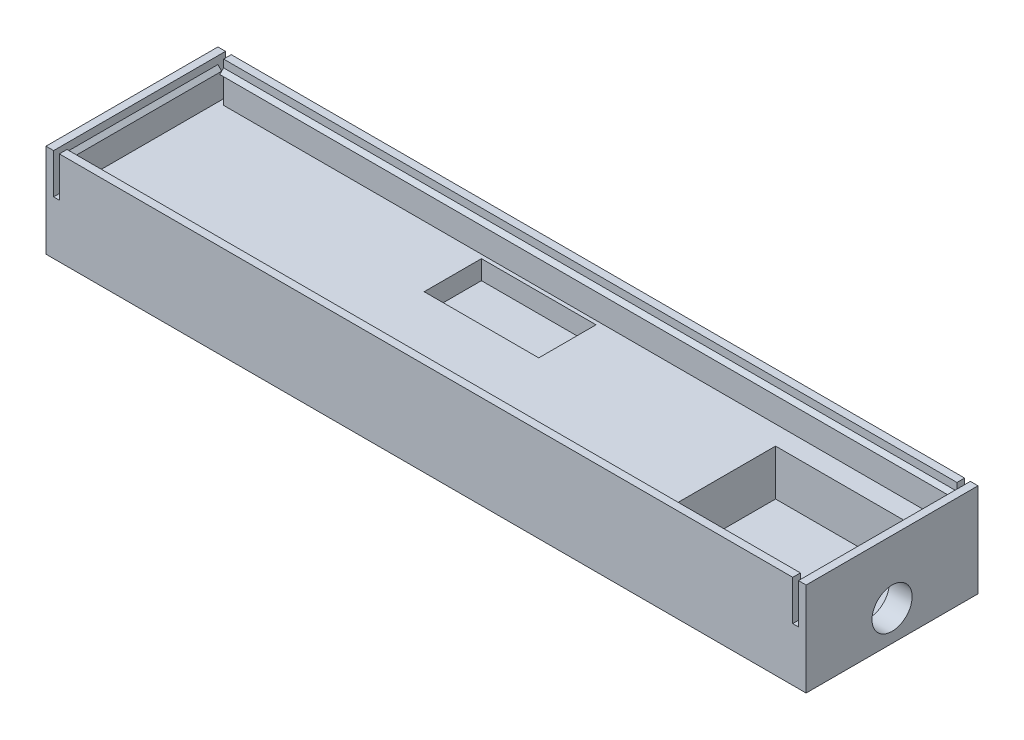
SolidWorks part; units mm, degrees
ref_plane "Front" through (0, 0, 0) normal (0, 0, 1) x (1, 0, 0)
ref_plane "Top" through (0, 0, 0) normal (0, 1, 0) x (1, 0, 0)
ref_plane "Right" through (0, 0, 0) normal (1, 0, 0) x (0, 0, -1)
sketch "Sketch1" plane through (0, 0, 0) normal (0, 1, 0) x (1, 0, 0)
  line L1 (-99.5, 22.5) -> (99.5, 22.5)
  line L2 (-99.5, 22.5) -> (-99.5, -22.5)
  line L3 (-99.5, -22.5) -> (99.5, -22.5)
  line L4 (99.5, 22.5) -> (99.5, -22.5)
  line L5 (-99.5, 22.5) -> (99.5, -22.5) construction
  line L6 (-99.5, -22.5) -> (99.5, 22.5) construction
  point P0 (0, 0)
  dimension "D1" = 45
  dimension "D2" = 199
extrude "Boss-Extrude1" add sketch "Sketch1" along normal blind 14
sketch "Sketch2" plane through (0, 14, 0) normal (0, 1, 0) x (1, 0, 0)
  line L0 (99.5, 22.5) -> (-99.5, 22.5) construction
  line L1 (93.5, 15.5) -> (53.5, 15.5)
  line L2 (93.5, 15.5) -> (93.5, -15.5)
  line L3 (93.5, -15.5) -> (53.5, -15.5)
  line L4 (53.5, 15.5) -> (53.5, -15.5)
  line L5 (99.5, -22.5) -> (99.5, 22.5) construction
  line L6 (-99.5, -22.5) -> (99.5, -22.5) construction
  line L8 (93.5, 15.5) -> (88.5, 15.5)
  line L9 (93.5, 15.5) -> (93.5, 10.5)
  line L10 (93.5, 10.5) -> (88.5, 10.5)
  line L11 (88.5, 15.5) -> (88.5, 10.5)
  line L12 (93.5, -15.5) -> (88.5, -15.5)
  line L13 (93.5, -15.5) -> (93.5, -10.5)
  line L14 (93.5, -10.5) -> (88.5, -10.5)
  line L15 (88.5, -15.5) -> (88.5, -10.5)
  dimension "D1" = 7
  dimension "D2" = 6
  dimension "D3" = 7
  dimension "D4" = 40
  dimension "D5" = 5
  dimension "D6" = 5
  dimension "D7" = 5
  dimension "D8" = 5
extrude "Cut-Extrude1" cut sketch "Sketch2" against normal blind 12 contours L3 L15 L14 L2 L10 L11 L1 L4
sketch "Sketch3" plane through (99.5, 0, 0) normal (1, 0, 0) x (0, 0, -1)
  line L0 (0, 0) -> (0, 50000) construction
  line L1 (-22.5, 14) -> (22.5, 14) construction
  circle A0 centre (0, 8) radius 5.25
  dimension "D1" = 10.5
  dimension "D2" = 6
extrude "Cut-Extrude2" cut sketch "Sketch3" against normal up to next
sketch "Sketch4" plane through (0, 14, 0) normal (0, 1, 0) x (1, 0, 0)
  line L0 (99.5, 22.5) -> (-99.5, 22.5) construction
  line L1 (-27.5, 19.5) -> (2.5, 19.5)
  line L2 (-27.5, 19.5) -> (-27.5, 4.5)
  line L3 (-27.5, 4.5) -> (2.5, 4.5)
  line L4 (2.5, 19.5) -> (2.5, 4.5)
  line L5 (-99.5, 22.5) -> (-99.5, -22.5) construction
  dimension "D1" = 30
  dimension "D2" = 15
  dimension "D3" = 3
  dimension "D4" = 72
extrude "Cut-Extrude3" cut sketch "Sketch4" against normal blind 5
sketch "Sketch5" plane through (0, 14, 0) normal (0, 1, 0) x (1, 0, 0)
  line L1 (-99.5, 22.5) -> (99.5, 22.5)
  line L2 (-99.5, 22.5) -> (-99.5, -22.5)
  line L3 (-99.5, -22.5) -> (99.5, -22.5)
  line L4 (99.5, 22.5) -> (99.5, -22.5)
  line L5 (-99.5, 22.5) -> (99.5, -22.5) construction
  line L6 (-99.5, -22.5) -> (99.5, 22.5) construction
  line L7 (-97.5, 20.5) -> (97.5, 20.5)
  line L8 (-97.5, 20.5) -> (-97.5, -20.5)
  line L9 (-97.5, -20.5) -> (97.5, -20.5)
  line L10 (97.5, 20.5) -> (97.5, -20.5)
  line L11 (-97.5, 20.5) -> (97.5, -20.5) construction
  line L12 (-97.5, -20.5) -> (97.5, 20.5) construction
  point P0 (0, 0)
  point P5 (0, 0)
  dimension "D1" = 2
  dimension "D2" = 2
extrude "Boss-Extrude2" add sketch "Sketch5" along normal blind 10.5
sketch "Sketch6" plane through (0, 24.5, 0) normal (0, 1, 0) x (1, 0, 0)
  line L0 (99.5, 22.5) -> (-99.5, 22.5) construction
  line L5 (-97.5, 20.5) -> (-96, 20.5)
  line L6 (-97.5, 20.5) -> (-97.5, 22.5)
  line L7 (-97.5, 22.5) -> (-96, 22.5)
  line L8 (-96, 20.5) -> (-96, 22.5)
  line L9 (0, 0) -> (0, 50000) construction
  line L10 (0, 0) -> (50000, 0) construction
  line L11 (97.5, 22.5) -> (96, 22.5)
  line L12 (96, 20.5) -> (96, 22.5)
  line L13 (97.5, 20.5) -> (96, 20.5)
  line L14 (97.5, 20.5) -> (97.5, 22.5)
  line L15 (97.5, -20.5) -> (97.5, -22.5)
  line L16 (97.5, -20.5) -> (96, -20.5)
  line L17 (96, -20.5) -> (96, -22.5)
  line L18 (97.5, -22.5) -> (96, -22.5)
  line L19 (-97.5, -22.5) -> (-96, -22.5)
  line L20 (-96, -20.5) -> (-96, -22.5)
  line L21 (-97.5, -20.5) -> (-96, -20.5)
  line L22 (-97.5, -20.5) -> (-97.5, -22.5)
  dimension "D1" = 1.5
extrude "Cut-Extrude4" cut sketch "Sketch6" against normal up to surface (10.5 mm away) up to face at (0, 14, 0)
sketch "Sketch7" plane through (0, 0, -20.5) normal (0, 0, 1) x (1, 0, 0)
  line L0 (-97.5, 22.5001) -> (-96.5, 21.5001)
  line L1 (-97.5, 14) -> (-97.5, 24.5) construction
  line L2 (-96.5, 21.5001) -> (-97.5, 20.5001)
  line L3 (-97.5, 20.5001) -> (-97.5, 22.5001)
  line L4 (-99.5, 24.5) -> (-97.5, 24.5) construction
  line L5 (0, 0) -> (0, 50000) construction
  line L6 (97.5, 20.5001) -> (97.5, 22.5001)
  line L7 (96.5, 21.5001) -> (97.5, 20.5001)
  line L8 (97.5, 22.5001) -> (96.5, 21.5001)
  dimension "D1" = 45
  dimension "D2" = 2
  dimension "D3" = 1.9999
extrude "Boss-Extrude5" add sketch "Sketch7" along normal up to surface (41 mm away) up to face at (0, 19.25, 20.5)
sketch "Sketch8" plane through (96, 0, 0) normal (1, 0, 0) x (0, 0, -1)
  line L0 (-20.5, 22.5) -> (-19.5, 21.5)
  line L1 (-20.5, 14) -> (-20.5, 24.5) construction
  line L2 (-19.5, 21.5) -> (-20.5, 20.5)
  line L3 (-20.5, 20.5) -> (-20.5, 22.5)
  line L4 (-22.5, 24.5) -> (22.5, 24.5) construction
  line L5 (0, 0) -> (0, 50000) construction
  line L6 (20.5, 20.5) -> (20.5, 22.5)
  line L7 (19.5, 21.5) -> (20.5, 20.5)
  line L8 (20.5, 22.5) -> (19.5, 21.5)
  dimension "D1" = 45
  dimension "D2" = 45
  dimension "D3" = 2
  dimension "D4" = 2
extrude "Boss-Extrude6" add sketch "Sketch8" against normal up to surface (192 mm away) up to face at (-96, 19.25, 21.5)
sketch "Sketch9" plane through (0, 0, 0) normal (0, -1, 0) x (1, 0, 0)
  line L0 (0, 0) -> (0, -50000) construction
  line L1 (0, 0) -> (50000, 0) construction
  line L2 (-99.5, 22.5) -> (99.5, 22.5) construction
  line L3 (-99.5, -22.5) -> (-99.5, 22.5) construction
  circle A0 centre (-93.5, 16.5) radius 3.5
  circle A1 centre (-93.5, -16.5) radius 3.5
  circle A2 centre (93.5, -16.5) radius 3.5
  circle A3 centre (93.5, 16.5) radius 3.5
  dimension "D1" = 7
  dimension "D2" = 6
  dimension "D3" = 6
extrude "Cut-Extrude5" cut sketch "Sketch9" against normal blind 8
